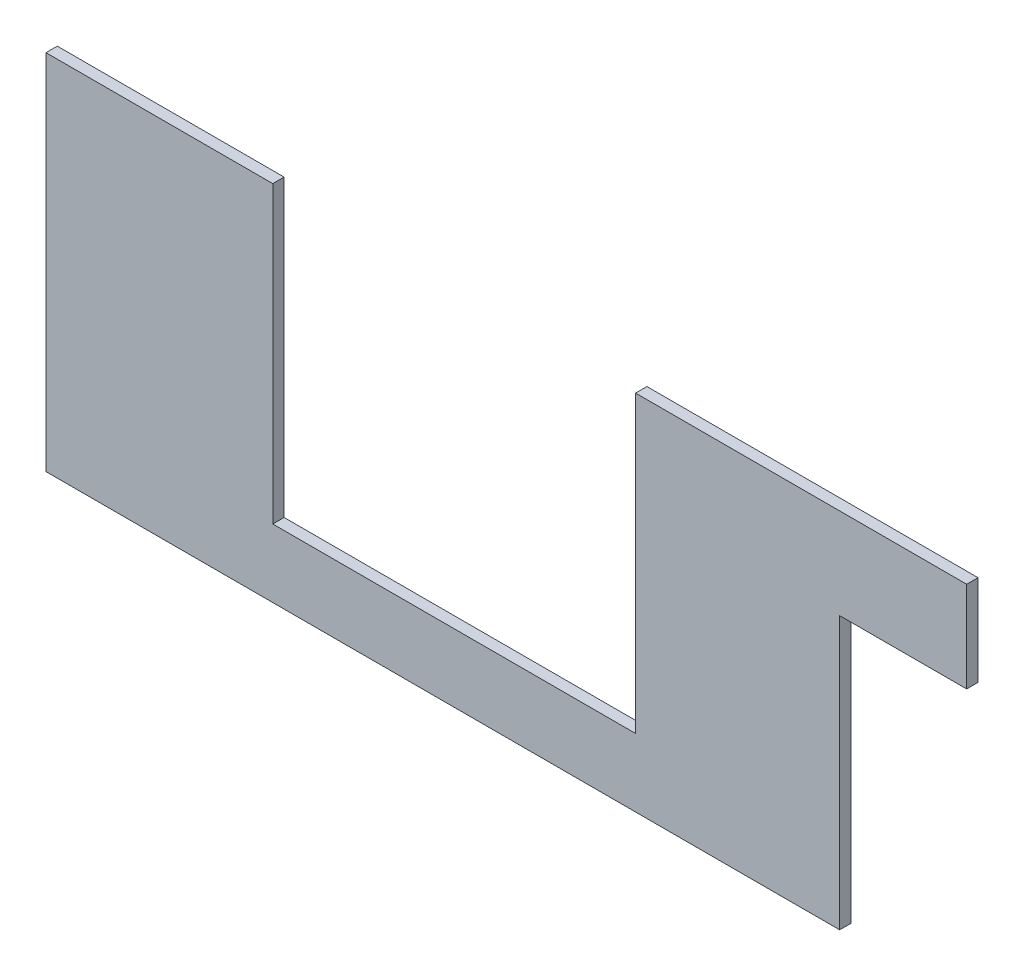
SolidWorks part; units mm, degrees
ref_plane "Front Plane" through (0, 0, 0) normal (0, 0, 1) x (1, 0, 0)
ref_plane "Top Plane" through (0, 0, 0) normal (0, 1, 0) x (1, 0, 0)
ref_plane "Right Plane" through (0, 0, 0) normal (1, 0, 0) x (0, 0, -1)
sketch "Sketch1" plane through (0, 0, 0) normal (0, 0, 1) x (1, 0, 0)
  line L0 (257.81, 76.2) -> (222.25, 76.2)
  line L1 (0, 0) -> (222.25, 0)
  line L2 (0, 0) -> (0, 101.6)
  line L3 (0, 101.6) -> (63.5, 101.6)
  line L4 (257.81, 76.2) -> (257.81, 101.6)
  line L5 (222.25, 76.2) -> (222.25, 0)
  line L6 (63.5, 101.6) -> (63.5, 19.05)
  line L7 (63.5, 19.05) -> (165.1, 19.05)
  line L8 (165.1, 19.05) -> (165.1, 101.6)
  line L9 (165.1, 101.6) -> (257.81, 101.6)
  dimension "D1" = 257.81
  dimension "D2" = 101.6
  dimension "D3" = 35.56
  dimension "D4" = 76.2
  dimension "D5" = 82.55
  dimension "D6" = 101.6
  dimension "D7" = 63.5
extrude "Boss-Extrude1" add sketch "Sketch1" along normal blind 3.175
